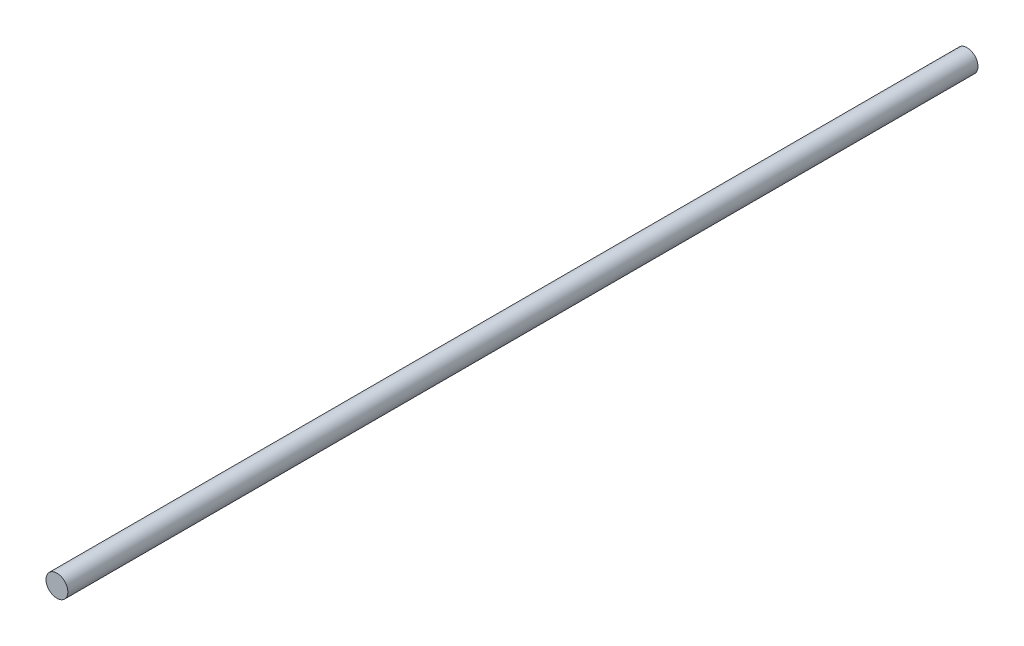
SolidWorks part; units mm, degrees
ref_plane "Front Plane" through (0, 0, 0) normal (0, 0, 1) x (1, 0, 0)
ref_plane "Top Plane" through (0, 0, 0) normal (0, 1, 0) x (1, 0, 0)
ref_plane "Right Plane" through (0, 0, 0) normal (1, 0, 0) x (0, 0, -1)
sketch "Sketch1" plane through (0, 0, 0) normal (0, 0, 1) x (1, 0, 0)
  circle A0 centre (0, 0) radius 3
  dimension "D1" = 6
extrude "Boss-Extrude1" add sketch "Sketch1" along normal blind 250
